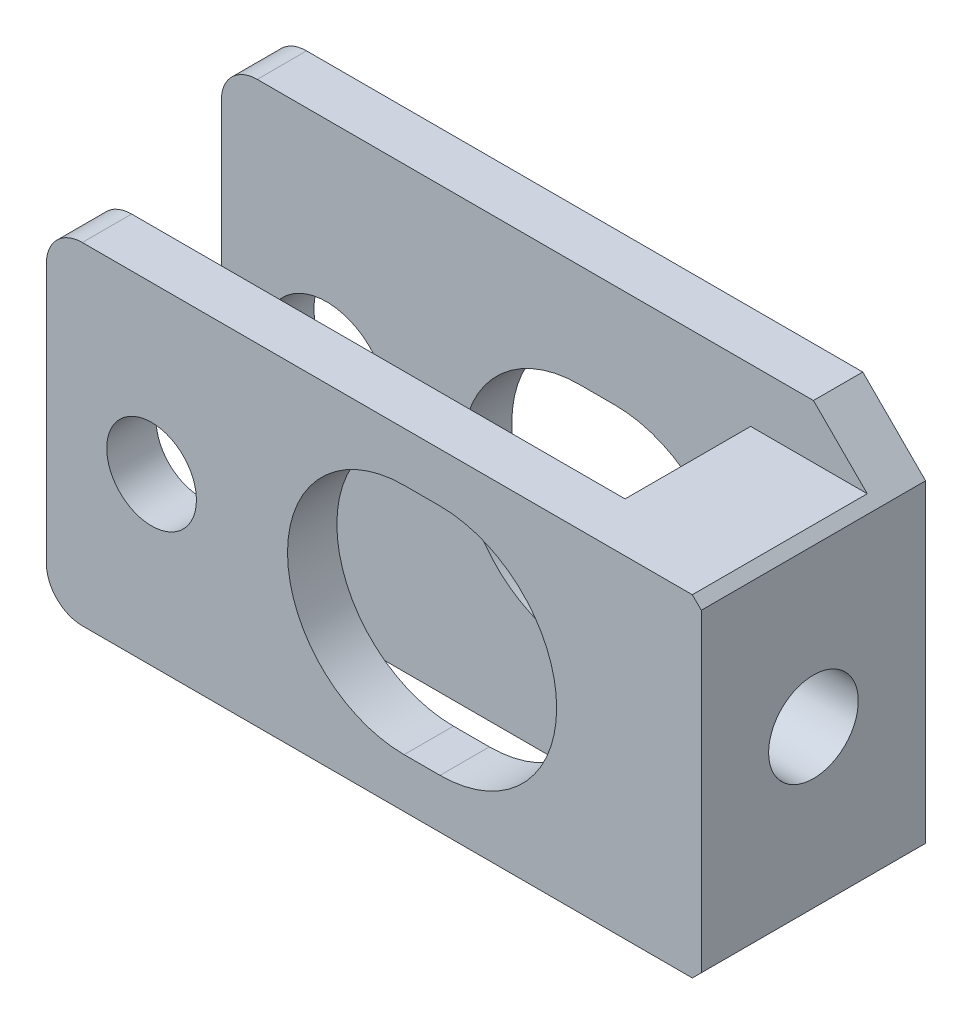
SolidWorks part; units mm, degrees
ref_plane "Front Plane" through (0, 0, 0) normal (0, 0, 1) x (1, 0, 0)
ref_plane "Top Plane" through (0, 0, 0) normal (0, 1, 0) x (1, 0, 0)
ref_plane "Right Plane" through (0, 0, 0) normal (1, 0, 0) x (0, 0, -1)
sketch "Sketch1" plane through (0, 0, 0) normal (0, 0, 1) x (1, 0, 0)
  line L0 (234.0556, 227.816) -> (270.5556, 227.816) construction
  line L1 (234.0556, 237.066) -> (270.5556, 237.066)
  line L2 (270.5556, 218.566) -> (270.5556, 237.066)
  line L3 (234.0556, 218.566) -> (270.5556, 218.566)
  line L4 (253.9933, 221.316) -> (255.9933, 221.316)
  line L5 (253.9933, 234.316) -> (255.9933, 234.316)
  line L50 (234.0556, 237.066) -> (234.0556, 218.566)
  arc A1 (253.9933, 234.316) -> (253.9933, 221.316) centre (253.9933, 227.816) ccw
  arc A2 (255.9933, 221.316) -> (255.9933, 234.316) centre (255.9933, 227.816) ccw
  circle A139 centre (239.916, 227.816) radius 3.45
  dimension "D11" = 6.9
  dimension "D2" = 36.5
  dimension "D5" = 9.25
  dimension "D4" = 18.5
extrude "Boss-Extrude1" add sketch "Sketch1" along normal blind 12.5
sketch "Sketch2" plane through (0, 237.066, 0) normal (0, 1, 0) x (1, 0, 0)
  line L0 (234.0556, -6.25) -> (270.5556, -6.25) construction
  line L1 (234.0556, -12.5) -> (234.0556, 0) construction
  line L2 (270.5556, -12.5) -> (270.5556, 0) construction
  line L3 (234.0556, -9.75) -> (263.5556, -9.75)
  line L4 (234.0556, -2.75) -> (263.5556, -2.75)
  line L5 (263.5556, -2.75) -> (263.5556, -9.75)
  line L6 (234.0556, -2.75) -> (234.0556, -9.75)
  line L7 (234.0556, -2.75) -> (270.5556, -2.75) construction
  line L8 (234.0556, -9.75) -> (270.5556, -9.75) construction
  dimension "D3" = 7
  dimension "D1" = 3.5
  dimension "D2" = 3.5
extrude "Cut-Extrude1" cut sketch "Sketch2" against normal through all
sketch "Sketch3" plane through (0, 0, 12.5) normal (0, 0, 1) x (1, 0, 0)
  circle A0 centre (239.916, 227.816) radius 3.45
  circle A1 centre (239.916, 227.816) radius 2.5
  dimension "D1" = 5
extrude "Boss-Extrude3" add sketch "Sketch3" against normal blind 2.75
sketch "Sketch4" plane through (0, 237.066, 0) normal (0, 1, 0) x (1, 0, 0)
  line L0 (234.0556, 0) -> (270.5556, 0)
  line L1 (234.0556, 0) -> (234.0556, -2.75)
  line L2 (234.0556, -2.75) -> (270.5556, -2.75)
  line L3 (270.5556, -12.5) -> (270.5556, 0) construction
  line L4 (270.5556, -2.75) -> (270.5556, 0)
extrude "Boss-Extrude4" add sketch "Sketch4" along normal blind 3
sketch "Sketch5" plane through (0, 218.566, 0) normal (0, -1, 0) x (1, 0, 0)
  line L0 (234.0556, 2.75) -> (270.5556, 2.75)
  line L1 (270.5556, 12.5) -> (270.5556, 0) construction
  line L2 (270.5556, 2.75) -> (270.5556, 0)
  line L3 (270.5556, 0) -> (234.0556, 0)
  line L4 (234.0556, 0) -> (234.0556, 2.75)
extrude "Boss-Extrude5" add sketch "Sketch5" along normal blind 3
chamfer "Chamfer1" distance 3.5 angle 45 1 edges at (270.5556, 215.566, 1.375)
chamfer "Chamfer3" distance 3.5 angle 45 1 edges at (270.5556, 240.066, 1.375)
sketch "Sketch6" plane through (263.5556, 0, 0) normal (-1, 0, 0) x (0, 0, 1)
  line L0 (2.75, 227.816) -> (9.75, 227.816) construction
  line L1 (2.75, 215.566) -> (2.75, 240.066) construction
  line L2 (9.75, 218.566) -> (9.75, 237.066) construction
  line L4 (6.25, 224.0054) -> (9.55, 225.9107)
  line L5 (9.55, 225.9107) -> (9.55, 229.7212)
  line L6 (9.55, 229.7212) -> (6.25, 231.6265)
  line L7 (6.25, 231.6265) -> (2.95, 229.7212)
  line L8 (2.95, 229.7212) -> (2.95, 225.9107)
  line L9 (2.95, 225.9107) -> (6.25, 224.0054)
  circle A0 centre (6.25, 227.816) radius 3.3 construction
  dimension "D1" = 6.6
extrude "Cut-Extrude2" cut sketch "Sketch6" against normal blind 3
sketch "Sketch7" plane through (266.5556, 0, 0) normal (-1, 0, 0) x (0, 0, 1)
  line L0 (2.95, 227.816) -> (9.55, 227.816) construction
  line L1 (2.95, 229.7212) -> (2.95, 225.9107) construction
  line L2 (9.55, 225.9107) -> (9.55, 229.7212) construction
  circle A0 centre (6.25, 227.816) radius 2.5
  dimension "D1" = 5
extrude "Cut-Extrude3" cut sketch "Sketch7" against normal through all
fillet "Fillet1" radius 2 4 edges at (234.0556, 240.066, 1.375) (234.0556, 237.066, 11.125) (234.0556, 218.566, 11.125) (234.0556, 215.566, 1.375)
